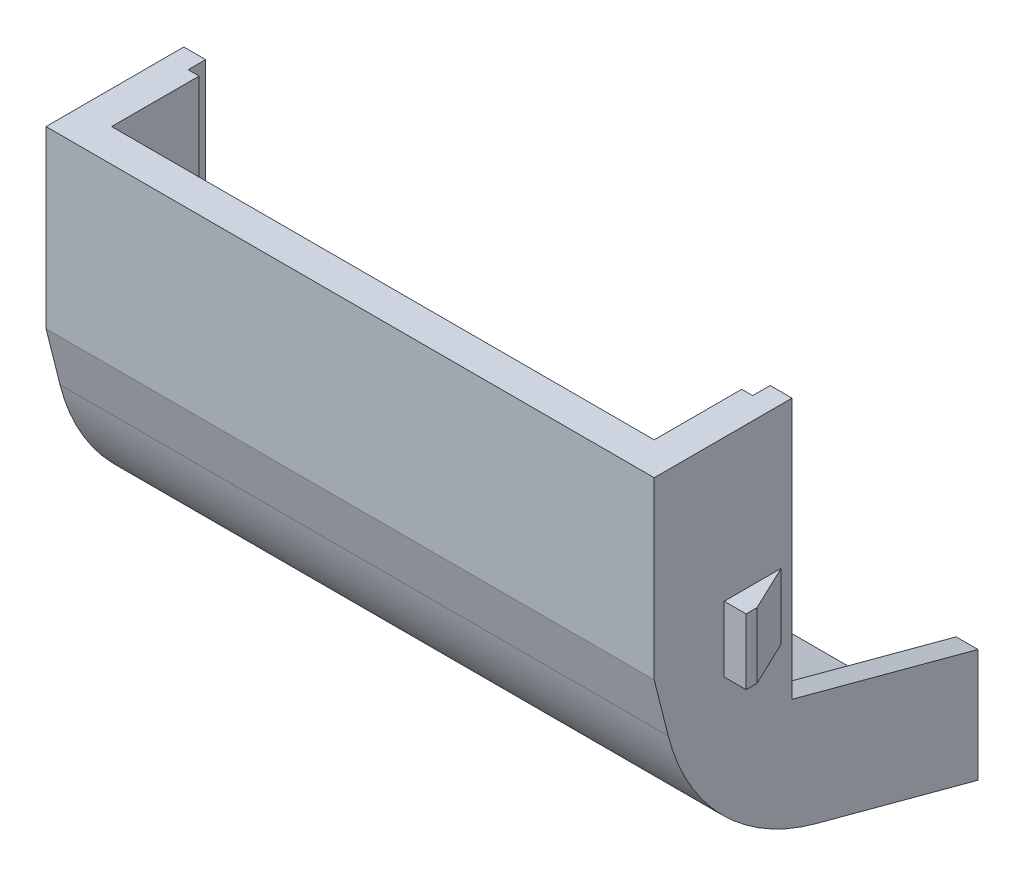
SolidWorks part; units mm, degrees
ref_plane "前视基准面" through (0, 0, 0) normal (0, 0, 1) x (1, 0, 0)
ref_plane "上视基准面" through (0, 0, 0) normal (0, 1, 0) x (1, 0, 0)
ref_plane "右视基准面" through (0, 0, 0) normal (1, 0, 0) x (0, 0, -1)
sketch "草图1" plane through (0, 0, 0) normal (0, 0, 1) x (1, 0, 0)
  line L0 (0, 0) -> (27.8, 0)
  line L1 (27.8, 0) -> (27.8, -8)
  line L2 (27.8, -8) -> (0, -8)
  line L3 (0, -8) -> (0, 0)
  line L4 (0, 0) -> (0.194, -0.0613)
  dimension "D1" = 27.8
  dimension "D2" = 8
extrude "凸台-拉伸1" add sketch "草图1" along normal blind 7.8
sketch "草图2" plane through (0, 0, 0) normal (-1, 0, 0) x (0, 0, 1)
  line L0 (5.7956, -15.9471) -> (0, -17.5)
  line L1 (0, -8) -> (0, -17.5)
  line L2 (7.8, -8) -> (5.7956, -15.9471)
  line L3 (0, -8) -> (7.8, -8)
  dimension "D1" = 75
  dimension "D2" = 9.5
  dimension "D3" = 6
extrude "凸台-拉伸2" add sketch "草图2" against normal up to surface (27.8 mm away) up to face at (27.8, -4, 3.9)
ref_plane "基准面1" through (0, 0, -1.9) normal (0, 0, -1) x (-1, 0, 0)
sketch "草图4" plane through (0, 0, -1.9) normal (0, 0, -1) x (-1, 0, 0)
  line L0 (0, 0) -> (0, -2) construction
  line L1 (0, -2) -> (5.3571, -2) construction
  line L3 (5.3571, 0) -> (0, 0) construction
  line L4 (0, -2) -> (0, -4.7)
  line L5 (0, -4.7) -> (6, -4.7)
  line L6 (6.5, -4.2) -> (6.5, -2)
  line L7 (1, -2) -> (0, -2)
  line L8 (1.5, -1.5) -> (1.5, 0.4)
  line L9 (4, 2.9) -> (6, 2.9)
  line L10 (6.5, 2.4) -> (6.5, -2)
  line L11 (0, 0) -> (-27.8, 0) construction
  arc A0 (1.5, 0.4) -> (4, 2.9) centre (4, 0.4) cw
  circle A1 centre (3.6, 0.5) radius 1.15
  arc A2 (6, 2.9) -> (6.5, 2.4) centre (6, 2.4) cw
  arc A3 (1.5, -1.5) -> (1, -2) centre (1, -1.5) cw
  arc A4 (6, -4.7) -> (6.5, -4.2) centre (6, -4.2) ccw
  dimension "D1" = 3.6
  dimension "D7" = 2.5
  dimension "D8" = 0.5
  dimension "D9" = 0.5
  dimension "D2" = 5.2
  dimension "D5" = 7.6
  dimension "D10" = 2.3
  dimension "D3" = 1.5
  dimension "D4" = 2
  dimension "D6" = 2.7
extrude "凸台-拉伸3" add sketch "草图4" against normal blind 2
ref_plane "基准面3" through (1.5, 0, 0) normal (-1, 0, 0) x (0, 0, 1)
ref_plane "基准面2" through (13.9, 0, 0) normal (-1, 0, 0) x (0, 0, 1)
mirror "镜向1" about plane through (13.9, 0, 0) normal (-1, 0, 0) of "凸台-拉伸3"
sketch "草图13" plane through (1.5, 0, 0) normal (-1, 0, 0) x (0, 0, 1)
  line L0 (1.5, 0) -> (1.5, -11.9217)
  line L1 (4.5565, -14.7262) -> (6.3, -7.8137)
  line L2 (1.5, 0) -> (6.3, 0)
  line L3 (6.3, 0) -> (6.3, -7.8137)
  line L4 (7.8, -8) -> (7.8, 0) construction
  line L5 (0, -17.5) -> (0, -4.7) construction
  line L6 (4.5565, -14.7262) -> (0, -15.9471)
  line L7 (1.5, -11.9217) -> (0, -12.3236)
  line L8 (0, -12.3236) -> (0, -15.9471)
  line L9 (0, -17.5) -> (5.7956, -15.9471) construction
  line L10 (7.8, 0) -> (0, 0) construction
  line L11 (5.7956, -15.9471) -> (7.8, -8) construction
  dimension "D1" = 1.5
  dimension "D5" = 1.5
  dimension "D2" = 1.5
  dimension "D3" = 1.5
  dimension "D4" = 3.5
extrude "切除-拉伸4" cut sketch "草图13" against normal blind 24.8
sketch "草图14" [suppressed] plane through (0, 0, 0) normal (0, 0, -1) x (-1, 0, 0)
  line L0 (-27.8, -1.5) -> (0, -1.5)
  line L1 (0, -1.5) -> (0, -3.5)
  line L2 (0, -17.5) -> (0, -4.7) construction
  line L3 (0, -3.5) -> (-27.8, -3.5)
  line L4 (-27.8, -1.5) -> (-27.8, -2) construction
  line L5 (-27.8, -3.5) -> (-27.8, -1.5)
  dimension "D1" = 2
extrude "切除-拉伸5" [suppressed] cut sketch "草图14" against normal blind 10
sketch "草图15" plane through (0, 0, 0) normal (0, 0, -1) x (-1, 0, 0)
  line L0 (-27.8, -2) -> (0, -2)
  line L1 (0, -2) -> (0, -6.2518)
  line L2 (0, -17.5) -> (0, -4.7) construction
  line L3 (0, -6.2518) -> (-27.8, -6.2518)
  line L4 (-27.8, -4.7) -> (-27.8, -17.5) construction
  line L5 (-27.8, -6.2518) -> (-27.8, -2)
extrude "凸台-拉伸4" add sketch "草图15" along normal up to surface (1.9 mm away) up to face at (31.0793, -1.0086, -1.9)
chamfer "倒角1" [suppressed] distance 1.9 angle 45
ref_plane "基准面4" through (13.9, 0, 0) normal (-1, 0, 0) x (0, 0, 1)
sketch "草图16" plane through (13.9, 0, 0) normal (-1, 0, 0) x (0, 0, 1)
  line L0 (4.5565, -14.7262) -> (-32.5836, -24.6778) construction
  line L1 (0, -15.9471) -> (4.5565, -14.7262) construction
  line L2 (-32.5495, -21.0452) -> (1.5, -11.9217) construction
  line L3 (1.5, -11.9217) -> (0, -12.3236) construction
fillet "圆角1" radius 8 1 edges at (13.9, -14.7262, 4.5565)
fillet "圆角2" radius 9.5 1 edges at (13.9, -15.9471, 5.7956)
sketch "草图17" plane through (27.8, 0, 0) normal (1, 0, 0) x (0, 0, -1)
  line L0 (0, -17.5) -> (7, -19.3756)
  line L1 (7, -19.3756) -> (7, -12.6463)
  line L2 (7, -12.6463) -> (0, -10.7707)
  line L3 (0, -6.2518) -> (0, -17.5) construction
  line L4 (0, -10.7707) -> (0, -17.5)
  line L5 (0, -17.5) -> (-0.4071, -17.3909) construction
  line L7 (-1.5, -11.9217) -> (0, -12.3236) construction
  dimension "D1" = 7
  dimension "D2" = 1.5
extrude "凸台-拉伸5" add sketch "草图17" against normal up to surface (27.8 mm away) up to face at (0, -6.6875, 1.7082)
sketch "草图18" plane through (26.3, 0, 0) normal (-1, 0, 0) x (0, 0, 1)
  line L0 (0, -12.3236) -> (0, -15.9471)
  line L1 (0, -15.9471) -> (-7, -17.8227)
  line L2 (-7, -17.8227) -> (-7, -14.1993)
  line L3 (-7, -14.1993) -> (0, -12.3236)
  line L4 (-7, -19.3756) -> (0.4071, -17.3909) construction
  line L5 (-7, -19.3756) -> (-7, -12.6463) construction
extrude "切除-拉伸6" cut sketch "草图18" along normal up to surface (24.8 mm away) up to face at (1.5, -9.3615, 2.7636)
sketch "草图19" plane through (34.3, 0, 0) normal (1, 0, 0) x (0, 0, -1)
  line L0 (7, 2.9) -> (7, -14.1993)
  line L1 (7, -19.3756) -> (7, -12.6463) construction
  line L2 (7, -14.1993) -> (-1.5, -11.9217)
  line L3 (-1.5, -11.9217) -> (-1.5, 2.9)
  line L5 (-1.5, -11.9217) -> (7, -14.1993) construction
  line L6 (-1.5, 2.9) -> (7, 2.9)
  line L7 (-1.5, 0) -> (-1.5, -11.9217) construction
  line L9 (-0.1, 2.9) -> (1.9, 2.9) construction
extrude "切除-拉伸7" cut sketch "草图19" against normal up to surface (40.8 mm away) up to face at (-6.5, -0.9, -0.9)
sketch "草图21" plane through (0, 0, 0) normal (-1, 0, 0) x (0, 0, 1)
  line L0 (2, -9.49) -> (4.6, -9.49)
  line L1 (4.6, -9.49) -> (4.6, -6.49)
  line L2 (4.6, -6.49) -> (2, -6.49)
  line L3 (2, -6.49) -> (2, -9.49)
  line L7 (1.5, -11.9217) -> (1.5, 0) construction
  line L8 (7.8, 0) -> (1.5, 0) construction
  dimension "D1" = 3
  dimension "D2" = 2.6
  dimension "D3" = 0.5
  dimension "D4" = 6.49
extrude "凸台-拉伸6" add sketch "草图21" along normal blind 1
sketch "草图22" plane through (0, -9.49, 0) normal (0, -1, 0) x (-1, 0, 0)
  line L0 (0, -2) -> (1, -4.1)
  line L1 (1, -2) -> (1, -4.6) construction
  line L2 (1, -4.1) -> (1, -2)
  line L3 (1, -2) -> (0, -2)
  line L4 (1, -4.6) -> (0, -4.6) construction
  dimension "D1" = 0.5
extrude "切除-拉伸8" cut sketch "草图22" along direction (0, -1, 0) on the side against the normal up to surface (3 mm away)
ref_plane "基准面5" through (13.9, 0, 0) normal (-1, 0, 0) x (0, 0, 1)
mirror "镜向5" about plane through (13.9, 0, 0) normal (-1, 0, 0) of "切除-拉伸8", "凸台-拉伸6"
sketch "草图23" plane through (26.3, 0, 0) normal (-1, 0, 0) x (0, 0, 1)
  line L0 (2.3, -12.5356) -> (-7, -15.0275)
  line L2 (2.3, 0) -> (1.5, 0)
  line L3 (1.5, 0) -> (1.5, -11.9217)
  line L4 (2.3, -12.5356) -> (-6.7929, -14.972)
  line L5 (2.3, 0) -> (2.3, -12.5356)
  line L6 (-7, -14.1993) -> (-7, -17.8227) construction
  line L7 (2.3, 0) -> (2.3, -12.5356)
  line L8 (-7, -15.0275) -> (-7, -14.1993)
  line L9 (-7, -14.1993) -> (1.5, -11.9217)
  dimension "D2" = 0.8
  dimension "D1" = 0.8
extrude "切除-拉伸9" cut sketch "草图23" against normal blind 0.5
mirror "镜向6" about plane through (13.9, 0, 0) normal (-1, 0, 0) of "切除-拉伸9"
